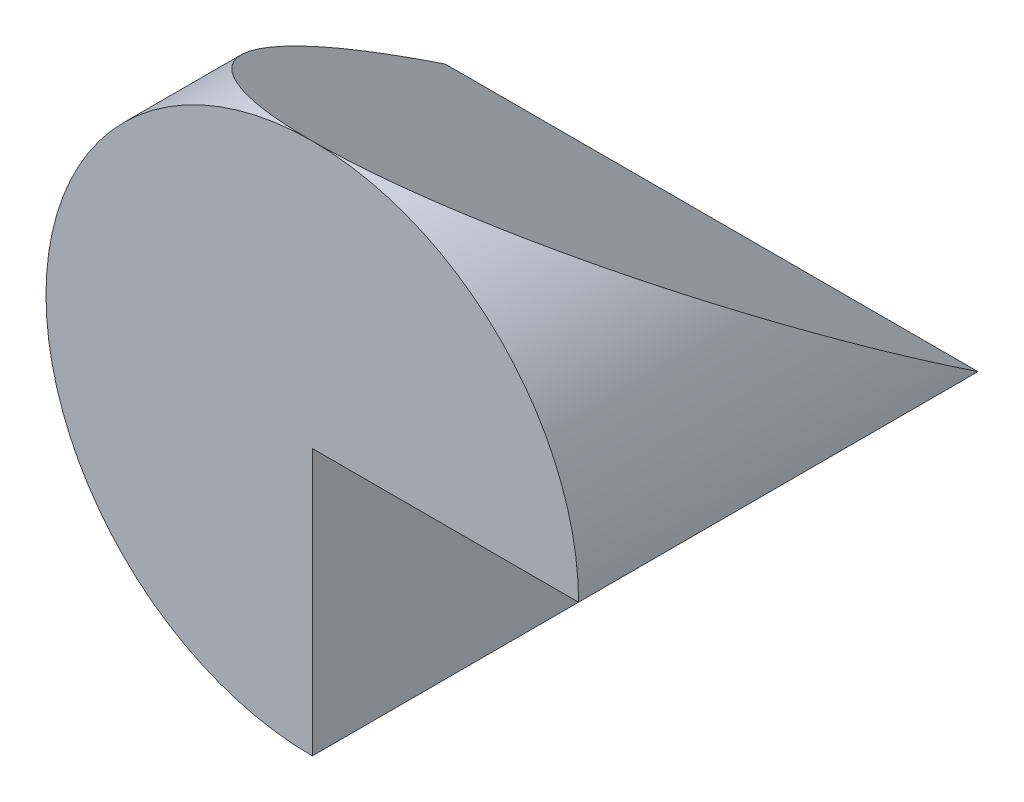
SolidWorks part; units mm, degrees
ref_plane "Front Plane" through (0, 0, 0) normal (0, 0, 1) x (1, 0, 0)
ref_plane "Top Plane" through (0, 0, 0) normal (0, 1, 0) x (1, 0, 0)
ref_plane "Right Plane" through (0, 0, 0) normal (1, 0, 0) x (0, 0, -1)
sketch "Sketch1" plane through (0, 0, 0) normal (0, 0, 1) x (1, 0, 0)
  circle A0 centre (0, 0) radius 10
  dimension "D1" = 20
extrude "Boss-Extrude1" add sketch "Sketch1" along normal blind 15
sketch "Sketch2" plane through (0, 0, 15) normal (0, 0, 1) x (1, 0, 0)
  line L0 (0, 0) -> (10, 0)
  line L1 (0, 0) -> (0, -10)
  circle A0 centre (0, 0) radius 10 construction
  arc A1 (0, -10) -> (10, 0) centre (0, 0) ccw
  circle M1 centre (0, 0) radius 10
extrude "Cut-Extrude1" cut sketch "Sketch2" against normal through all contours L0 L1 M1
ref_plane "Plane1" through (0, 10, 0) normal (0, 1, 0) x (1, 0, 0)
sketch "Sketch3" plane through (0, 10, 0) normal (0, 1, 0) x (1, 0, 0)
  point P0 (0, -14.8602)
ref_plane "Plane2" through (10, 0, 0) normal (1, 0, 0) x (0, 0, -1)
sketch "Sketch5" plane through (10, 0, 0) normal (1, 0, 0) x (0, 0, -1)
  line L0 (0, 0) -> (0, 10)
  line L1 (0, 10) -> (-15, 10)
  line L2 (-15, 10) -> (0, 0)
  dimension "D1" = 10
  dimension "D2" = 15
extrude "Cut-Extrude2" cut sketch "Sketch5" against normal blind 10
sketch "Sketch6" plane through (0, 0, 0) normal (1, 0, 0) x (0, 0, -1)
  line L0 (-15, 10) -> (0, 0)
  line L1 (0, 0) -> (0, 10)
  line L2 (0, 10) -> (-15, 10)
extrude "Cut-Extrude3" cut sketch "Sketch6" against normal blind 10
